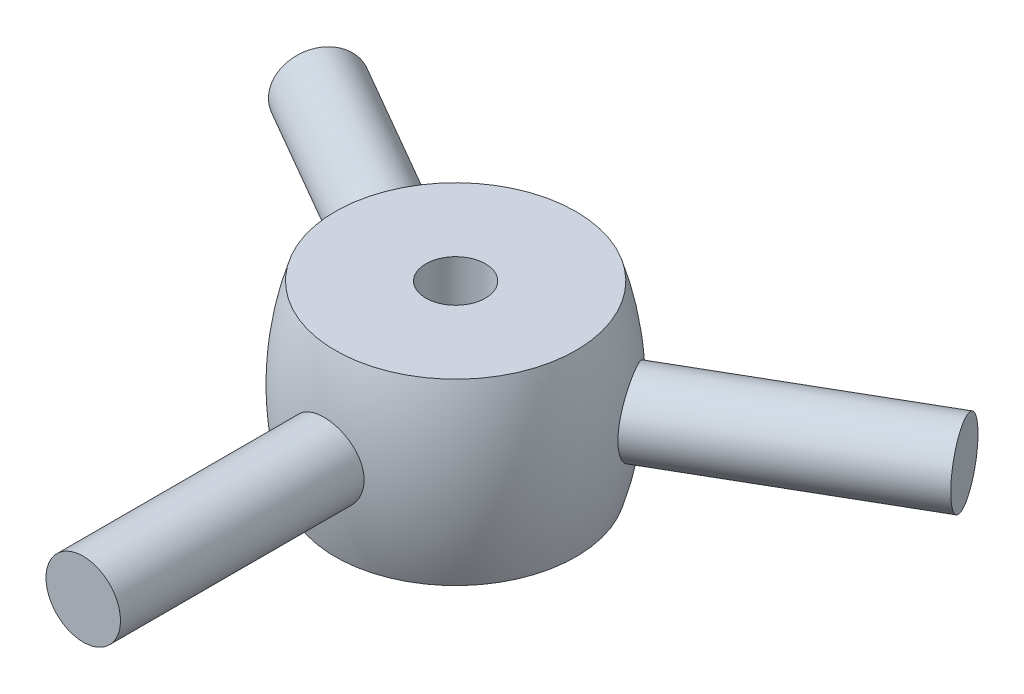
SolidWorks part; units mm, degrees
ref_plane "Plane1" through (0, 0, 0) normal (0, 0, 1) x (1, 0, 0)
ref_plane "Plane2" through (0, 0, 0) normal (0, 1, 0) x (1, 0, 0)
ref_plane "Plane3" through (0, 0, 0) normal (1, 0, 0) x (0, 0, -1)
sketch "Esquisse1" plane through (0, 0, 0) normal (0, 0, 1) x (1, 0, 0)
  line L0 (0, -3) -> (0, 39) construction
  line L1 (0, 3) -> (4.0394, 3)
  line L2 (0, -3) -> (4.0394, -3)
  line L3 (0, 3) -> (0, -3)
  arc A0 (4.0394, -3) -> (4.0394, 3) centre (-5.5, 0) ccw
  dimension "D1" = 20
revolve "Base-Révolution" add sketch "Esquisse1" angle 360 about L0
sketch "Esquisse2" plane through (0, -3, 0) normal (0, -1, 0) x (1, 0, 0)
  circle A0 centre (0, 0) radius 1
  dimension "D1" = 2
sketch "Esquisse3" plane through (0, 0, 0) normal (0, 0, 1) x (1, 0, 0)
  circle A0 centre (0, 0) radius 1.25
  dimension "D1" = 2.5
extrude "Boss.-Extru.1" add sketch "Esquisse3" along normal blind 12.5
pattern_circular "Répétition circulaire1" count 3 every 120 about axis through (0, -3, 0) along (0, 1, 0)
extrude "Enlèv. mat.-Extru.2" cut sketch "Esquisse2" against normal through all
